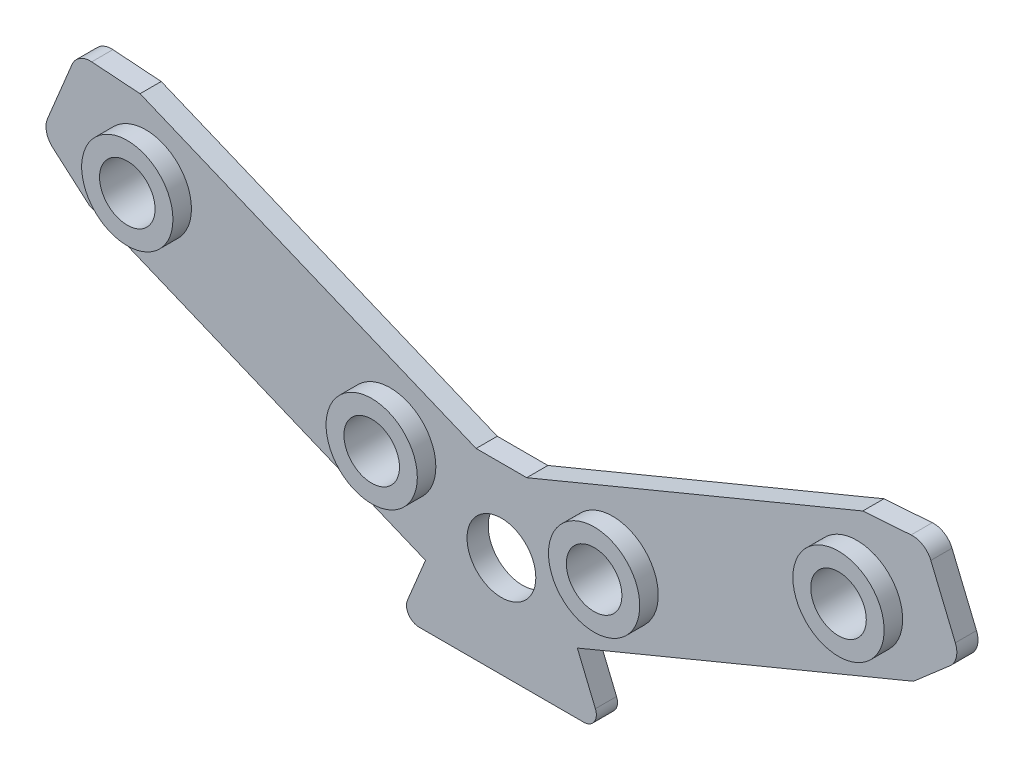
SolidWorks part; units mm, degrees
material "Plain Carbon Steel"
ref_plane "Front Plane" through (0, 0, 0) normal (0, 0, 1) x (1, 0, 0)
ref_plane "Top Plane" through (0, 0, 0) normal (0, 1, 0) x (1, 0, 0)
ref_plane "Right Plane" through (0, 0, 0) normal (1, 0, 0) x (0, 0, -1)
sketch "Sketch1" plane through (0, 0, 0) normal (0, 0, 1) x (1, 0, 0)
  line L0 (0, 0) -> (0, 67.9164) construction
  line L1 (-1.9135, 6.2046) -> (1.9135, 6.2046)
  line L2 (1.9135, 6.2046) -> (27.3202, 16.7284)
  line L3 (27.3202, 16.7284) -> (30.9733, 16.988)
  line L4 (32.4654, 16.0658) -> (34.3167, 11.5963)
  line L5 (33.3911, 13.831) -> (0, 0) construction
  line L6 (31.147, 7.4896) -> (33.9137, 9.8891)
  line L7 (5.7403, -3.0342) -> (31.147, 7.4896)
  line L8 (5.7403, -3.0342) -> (7.1039, -6.3263)
  line L9 (6.217, -7.6536) -> (-6.217, -7.6536)
  line L12 (-5.7403, -3.0342) -> (-7.1039, -6.3263)
  line L13 (-5.7403, -3.0342) -> (-31.147, 7.4896)
  line L14 (-31.147, 7.4896) -> (-33.9137, 9.8891)
  line L15 (-32.4654, 16.0658) -> (-34.3167, 11.5963)
  line L16 (-27.3202, 16.7284) -> (-30.9733, 16.988)
  line L17 (-1.9135, 6.2046) -> (-27.3202, 16.7284)
  circle A0 centre (0, 0) radius 2.6
  arc A1 (-33.9137, 9.8891) -> (-34.3167, 11.5963) centre (-32.9309, 11.0223) cw
  arc A2 (-32.4654, 16.0658) -> (-30.9733, 16.988) centre (-31.0796, 15.4917) cw
  arc A3 (30.9733, 16.988) -> (32.4654, 16.0658) centre (31.0796, 15.4917) cw
  arc A4 (33.9137, 9.8891) -> (34.3167, 11.5963) centre (32.9309, 11.0223) ccw
  arc A5 (-7.1039, -6.3263) -> (-6.217, -7.6536) centre (-6.217, -6.6936) ccw
  arc A6 (7.1039, -6.3263) -> (6.217, -7.6536) centre (6.217, -6.6936) cw
  point P13 (-7.6538, -7.6536)
  point P17 (7.6538, -7.6536)
  point P24 (0, 6.2046)
  point P26 (-34.7305, 10.5975)
  point P29 (-32.0517, 17.0646)
  point P32 (32.0517, 17.0646)
  point P35 (34.7305, 10.5975)
  dimension "D4" = 5
  dimension "D8" = 3.827
  dimension "D9" = 0.96
  dimension "D11" = 1.5
  dimension "D1" = 5.2
  dimension "D2" = 10
  dimension "D3" = 67.5
  dimension "D5" = 32
  dimension "D6" = 4.5
  dimension "D7" = 7
extrude "Boss-Extrude1" add sketch "Sketch1" along normal blind 1.6
sketch "Sketch2" plane through (0, 0, 1.6) normal (0, 0, 1) x (1, 0, 0)
  line L0 (-33.3911, 13.831) -> (-7.2797, 3.0154) construction
  line L1 (-32.4654, 16.0658) -> (-34.3167, 11.5963) construction
  line L2 (0, 6.2046) -> (0, 26.5175) construction
  line L5 (-1.9135, 6.2046) -> (-27.3202, 16.7284) construction
  line L8 (1.9135, 6.2046) -> (-1.9135, 6.2046) construction
  line L9 (-8.4073, 3.4824) -> (-10.3207, -1.137) construction
  line L10 (-31.147, 7.4896) -> (-5.7403, -3.0342) construction
  circle A0 centre (26.8849, 11.1361) radius 3.45
  circle A1 centre (8.4073, 3.4824) radius 3.45
  circle A4 centre (-8.4073, 3.4824) radius 3.45
  circle A5 centre (-26.8849, 11.1361) radius 3.45
  dimension "D1" = 6.9
  dimension "D2" = 9.1
  dimension "D4" = 20
extrude "Boss-Extrude2" add sketch "Sketch2" along normal blind 1.4
hole_wizard "M5x0.8 Tapped Hole1" positions "Sketch4" profile "Sketch3" tap size "M5x0.8" standard "ANSI Metric" end condition through all
sketch "Sketch4" plane through (0, 0, 3) normal (0, 0, 1) x (1, 0, 0)
  point P0 (26.8849, 11.1361)
  point P3 (8.4073, 3.4824)
  point P13 (-8.4073, 3.4824)
  point P16 (-26.8849, 11.1361)
cosmetic thread "Hole Thread3" parameters "D2"=5
cosmetic thread "Hole Thread5" parameters "D2"=5
cosmetic thread "Hole Thread6" parameters "D2"=5
cosmetic thread "Hole Thread7" parameters "D2"=5
sketch "Sketch3" plane through (26.8849, 11.1361, 3) normal (1, 0, 0) x (0, -1, 0)
  line L0 (0, 0) -> (0, 3)
  line L1 (0, 3) -> (2.1, 3)
  line L2 (2.1, 3) -> (2.1, 0)
  line L5 (2.1, 0) -> (0, 0)
  line L11 (0, -6.35) -> (0, 107.95) construction
  dimension "Thru Tap Drill Dia." = 4.2
  dimension "Thru Tap Drill Depth" = 3
